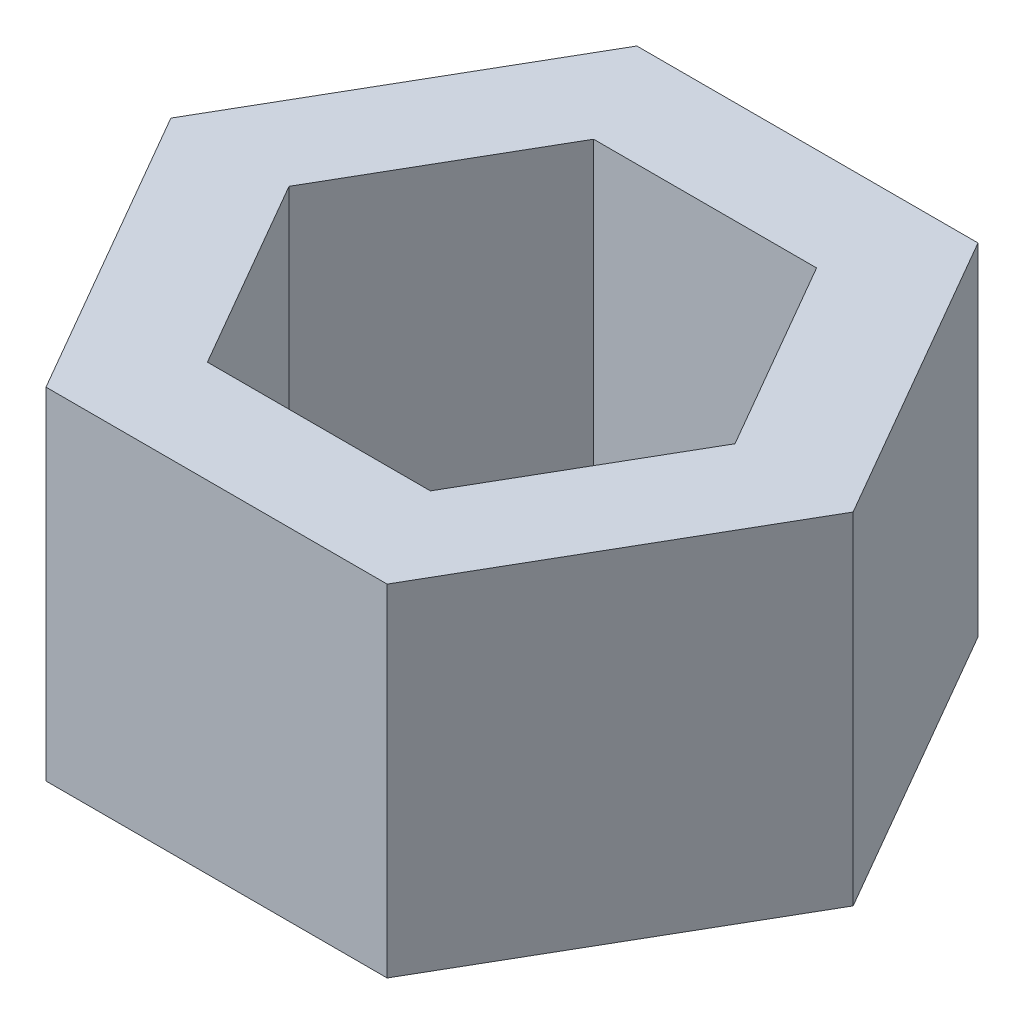
SolidWorks part; units mm, degrees
ref_plane "Front Plane" through (0, 0, 0) normal (0, 0, 1) x (1, 0, 0)
ref_plane "Top Plane" through (0, 0, 0) normal (0, 1, 0) x (1, 0, 0)
ref_plane "Right Plane" through (0, 0, 0) normal (1, 0, 0) x (0, 0, -1)
sketch "Sketch1" plane through (0, 0, 0) normal (0, 1, 0) x (1, 0, 0)
  line L1 (-25, -43.3013) -> (25, -43.3013)
  line L2 (25, -43.3013) -> (50, 0)
  line L3 (50, 0) -> (25, 43.3013)
  line L4 (25, 43.3013) -> (-25, 43.3013)
  line L5 (-25, 43.3013) -> (-50, 0)
  line L6 (-50, 0) -> (-25, -43.3013)
  circle A0 centre (0, 0) radius 43.3013 construction
  dimension "D1" = 50
extrude "Boss-Extrude1" add sketch "Sketch1" along normal blind 50
sketch "Sketch2" plane through (0, 50, 0) normal (0, 1, 0) x (1, 0, 0)
  line L12 (-32.6795, 0) -> (-16.3397, -28.3013)
  line L13 (-16.3397, -28.3013) -> (16.3397, -28.3013)
  line L14 (16.3397, -28.3013) -> (32.6795, 0)
  line L15 (32.6795, 0) -> (16.3397, 28.3013)
  line L16 (16.3397, 28.3013) -> (-16.3397, 28.3013)
  line L17 (-16.3397, 28.3013) -> (-32.6795, 0)
  line L18 (-32.6795, 0) -> (-16.3397, -28.3013)
  line L19 (-16.3397, -28.3013) -> (16.3397, -28.3013)
  line L20 (16.3397, -28.3013) -> (32.6795, 0)
  line L21 (32.6795, 0) -> (16.3397, 28.3013)
  line L22 (16.3397, 28.3013) -> (-16.3397, 28.3013)
  line L23 (-16.3397, 28.3013) -> (-32.6795, 0)
  dimension "D1" = 15
extrude "Cut-Extrude1" cut sketch "Sketch2" against normal through all
